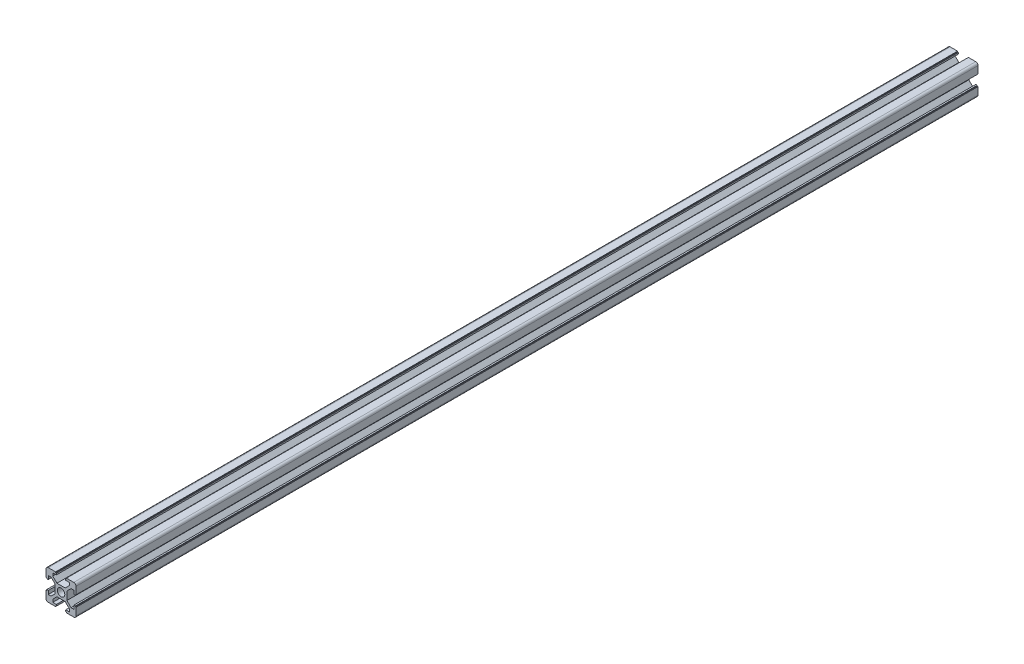
SolidWorks part; units mm, degrees
ref_plane "前视基准面" through (0, 0, 0) normal (0, 0, 1) x (1, 0, 0)
ref_plane "上视基准面" through (0, 0, 0) normal (0, 1, 0) x (1, 0, 0)
ref_plane "右视基准面" through (0, 0, 0) normal (1, 0, 0) x (0, 0, -1)
sketch "草图1" plane through (0, 0, 0) normal (0, 0, 1) x (1, 0, 0)
  line L0 (-3.6, 10) -> (-3.6, 9.5)
  line L1 (-3.6, 9.5) -> (-3.1, 9.5)
  line L2 (-3.1, 9.5) -> (-3.1, 8.5)
  line L3 (-3.1, 8.5) -> (-5.5, 8.5)
  line L4 (-8.5, -10) -> (-3.6, -10)
  line L5 (-10, -8.5) -> (-10, -3.6)
  line L6 (8.5, 10) -> (3.6, 10)
  line L7 (10, 8.5) -> (10, 3.6)
  line L8 (0, 14.8756) -> (0, 0) construction
  line L9 (0, 0) -> (14.1675, 0) construction
  line L10 (-5.5, 8.5) -> (-5.5, 6.65)
  line L11 (-5.5, 6.65) -> (-2.75, 3.9)
  line L12 (-2.75, 3.9) -> (2.75, 3.9)
  line L13 (5.5, 6.65) -> (2.75, 3.9)
  line L14 (5.5, 8.5) -> (5.5, 6.65)
  line L15 (3.1, 8.5) -> (5.5, 8.5)
  line L16 (3.1, 9.5) -> (3.1, 8.5)
  line L17 (3.6, 9.5) -> (3.1, 9.5)
  line L18 (3.6, 10) -> (3.6, 9.5)
  line L19 (-3.6, 10) -> (-8.5, 10)
  line L20 (10, 3.6) -> (9.5, 3.6)
  line L21 (9.5, 3.6) -> (9.5, 3.1)
  line L22 (9.5, 3.1) -> (8.5, 3.1)
  line L23 (8.5, 3.1) -> (8.5, 5.5)
  line L24 (8.5, 5.5) -> (6.65, 5.5)
  line L25 (6.65, 5.5) -> (3.9, 2.75)
  line L26 (3.9, 2.75) -> (3.9, -2.75)
  line L27 (6.65, -5.5) -> (3.9, -2.75)
  line L28 (8.5, -5.5) -> (6.65, -5.5)
  line L29 (8.5, -3.1) -> (8.5, -5.5)
  line L30 (9.5, -3.1) -> (8.5, -3.1)
  line L31 (9.5, -3.6) -> (9.5, -3.1)
  line L32 (10, -3.6) -> (9.5, -3.6)
  line L33 (3.6, -10) -> (3.6, -9.5)
  line L34 (3.6, -9.5) -> (3.1, -9.5)
  line L35 (3.1, -9.5) -> (3.1, -8.5)
  line L36 (3.1, -8.5) -> (5.5, -8.5)
  line L37 (5.5, -8.5) -> (5.5, -6.65)
  line L38 (5.5, -6.65) -> (2.75, -3.9)
  line L39 (2.75, -3.9) -> (-2.75, -3.9)
  line L40 (-5.5, -6.65) -> (-2.75, -3.9)
  line L41 (-5.5, -8.5) -> (-5.5, -6.65)
  line L42 (-3.1, -8.5) -> (-5.5, -8.5)
  line L43 (-3.1, -9.5) -> (-3.1, -8.5)
  line L44 (-3.6, -9.5) -> (-3.1, -9.5)
  line L45 (-3.6, -10) -> (-3.6, -9.5)
  line L46 (-10, -3.6) -> (-9.5, -3.6)
  line L47 (-9.5, -3.6) -> (-9.5, -3.1)
  line L48 (-9.5, -3.1) -> (-8.5, -3.1)
  line L49 (-8.5, -3.1) -> (-8.5, -5.5)
  line L50 (-8.5, -5.5) -> (-6.65, -5.5)
  line L51 (-6.65, -5.5) -> (-3.9, -2.75)
  line L52 (-3.9, -2.75) -> (-3.9, 2.75)
  line L53 (-6.65, 5.5) -> (-3.9, 2.75)
  line L54 (-8.5, 5.5) -> (-6.65, 5.5)
  line L55 (-8.5, 3.1) -> (-8.5, 5.5)
  line L56 (-9.5, 3.1) -> (-8.5, 3.1)
  line L57 (-9.5, 3.6) -> (-9.5, 3.1)
  line L58 (-10, 3.6) -> (-9.5, 3.6)
  line L59 (3.6, -10) -> (8.5, -10)
  line L60 (-10, 3.6) -> (-10, 8.5)
  line L61 (10, -3.6) -> (10, -8.5)
  circle A0 centre (0, 0) radius 2.5
  arc A1 (-10, 8.5) -> (-8.5, 10) centre (-8.5, 8.5) cw
  arc A2 (10, 8.5) -> (8.5, 10) centre (8.5, 8.5) ccw
  arc A3 (-8.5, -10) -> (-10, -8.5) centre (-8.5, -8.5) cw
  arc A4 (8.5, -10) -> (10, -8.5) centre (8.5, -8.5) ccw
  point P0 (-10, 0)
  point P1 (10, 0)
  point P2 (0, 10)
  point P3 (0, -10)
  point P4 (0, 0)
  point P5 (-10, -10)
  point P6 (10, -10)
  point P7 (10, 10)
  point P8 (-10, 10)
  point P13 (0, 0)
  dimension "D1" = 11
  dimension "D2" = 20
  dimension "D3" = 6.2
  dimension "D4" = 7.2
  dimension "D5" = 6.1
  dimension "D6" = 5
  dimension "D7" = 1.5
  dimension "D8" = 45
  dimension "D9" = 0.5
  dimension "D10" = 1
  dimension "D11" = 5.5
extrude "凸台-拉伸1" add sketch "草图1" along normal blind 600
